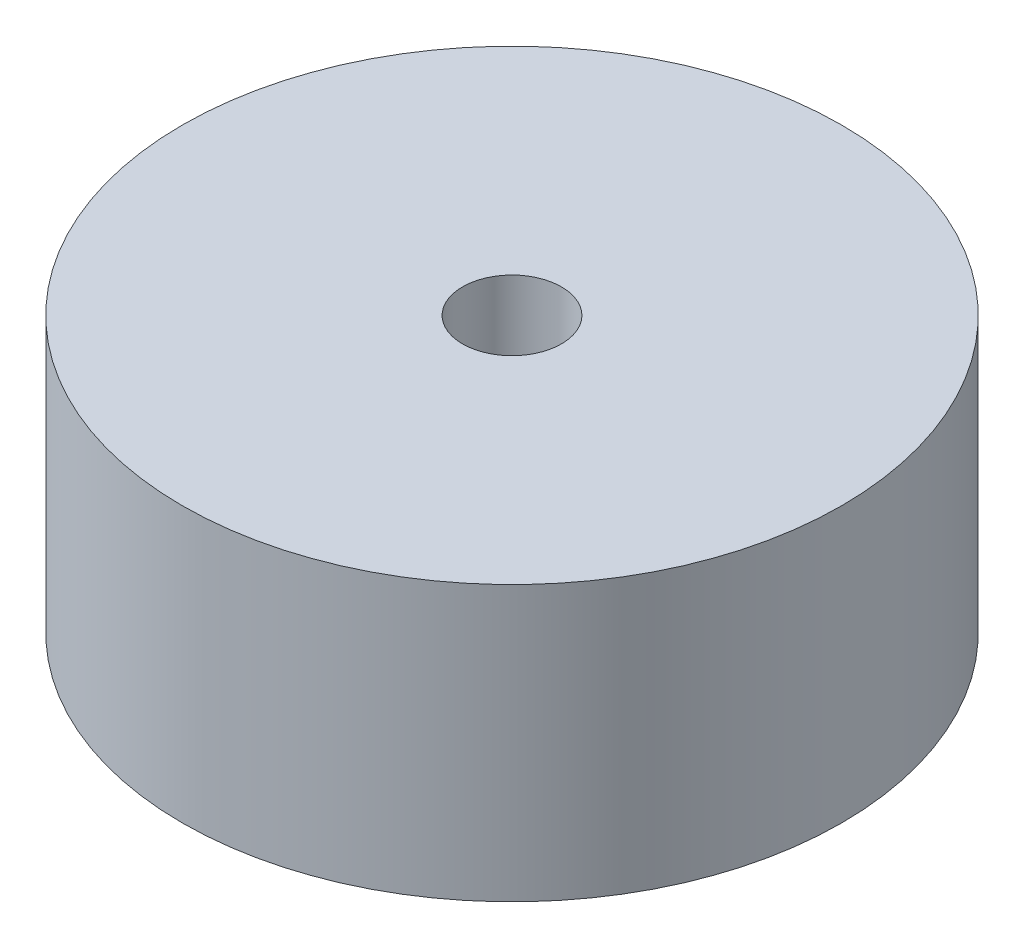
SolidWorks part; units mm, degrees
ref_plane "Front Plane" through (0, 0, 0) normal (0, 0, 1) x (1, 0, 0)
ref_plane "Top Plane" through (0, 0, 0) normal (0, 1, 0) x (1, 0, 0)
ref_plane "Right Plane" through (0, 0, 0) normal (1, 0, 0) x (0, 0, -1)
sketch "Sketch1" plane through (0, 0, 0) normal (0, 1, 0) x (1, 0, 0)
  circle A0 centre (0, 0) radius 60
  circle A1 centre (0, 0) radius 9
  dimension "D1" = 120
  dimension "D2" = 18
extrude "Boss-Extrude1" add sketch "Sketch1" along normal blind 50
